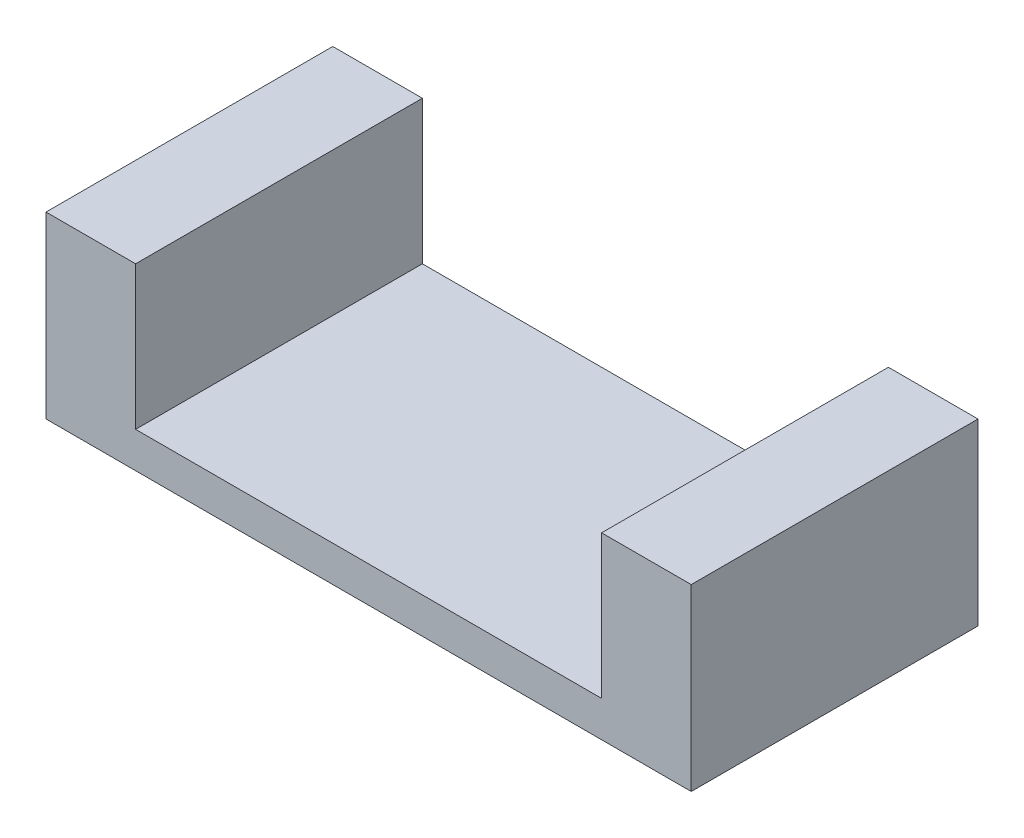
SolidWorks part; units mm, degrees
ref_plane "Front" through (0, 0, 0) normal (0, 0, 1) x (1, 0, 0)
ref_plane "Top" through (0, 0, 0) normal (0, 1, 0) x (1, 0, 0)
ref_plane "Right" through (0, 0, 0) normal (1, 0, 0) x (0, 0, -1)
sketch "Sketch4" plane through (0, 0, 0) normal (0, 0, 1) x (1, 0, 0)
  line L0 (-3.6, 1) -> (-3.1, 1)
  line L1 (0, 0) -> (-3.6, 0)
  line L2 (0, 0) -> (0, 1)
  line L3 (0, 1) -> (-0.5, 1)
  line L4 (-3.6, 0) -> (-3.6, 1)
  line L5 (0, 0) -> (-3.6, 1) construction
  line L6 (0, 1) -> (-3.6, 0) construction
  line L7 (-3.1, 1) -> (-3.1, 0.2)
  line L9 (-0.5, 1) -> (-0.5, 0.2)
  line L10 (-0.5, 0.2) -> (-3.1, 0.2)
  point P4 (-1.8, 0.5)
  dimension "D1" = 3.6
  dimension "D2" = 1
  dimension "D3" = 1
  dimension "D4" = 0.5
  dimension "D5" = 0.5
  dimension "D6" = 0.8
extrude "Boss-Extrude3" add sketch "Sketch4" along normal blind 1.6
